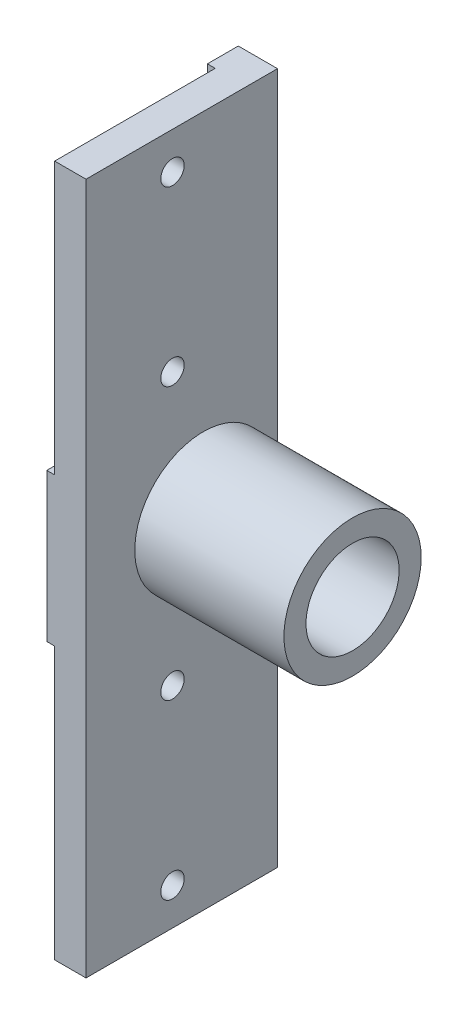
SolidWorks part; units mm, degrees
material "6061-T6 (SS)"
ref_plane "Front Plane" through (0, 0, 0) normal (0, 0, 1) x (1, 0, 0)
ref_plane "Top Plane" through (0, 0, 0) normal (0, 1, 0) x (1, 0, 0)
ref_plane "Right Plane" through (0, 0, 0) normal (1, 0, 0) x (0, 0, -1)
sketch "Sketch1" plane through (0, 0, 0) normal (1, 0, 0) x (0, 0, -1)
  line L0 (0, 0) -> (-63.5861, 0) construction
  line L1 (0, 0) -> (0, -23.8126) construction
  line L2 (12, 0) -> (12, 56)
  line L3 (12, 56) -> (-19, 56)
  line L4 (-19, 56) -> (-19, 0)
  line L5 (-19, 0) -> (12, 0)
  circle A1 centre (0, 0) radius 7.5413 construction
  dimension "D5" = 15.0825
  dimension "D3" = 31
  dimension "D4" = 112
  dimension "D6" = 12
extrude "Boss-Extrude1" add sketch "Sketch1" along normal blind 6.35
mirror "Mirror1" about plane through (0, 0, 0) normal (0, 1, 0) of "Boss-Extrude1"
sketch "Sketch2" plane through (6.35, 0, 0) normal (1, 0, 0) x (0, 0, -1)
  circle A0 centre (0, 0) radius 11.1125
  circle A2 centre (0, 0) radius 7.5413 construction
  dimension "D1" = 22.225
extrude "Boss-Extrude2" add sketch "Sketch2" along normal blind 24.1525
sketch "Sketch3" plane through (0, 0, 0) normal (-1, 0, 0) x (0, 0, 1)
  circle A0 centre (0, 0) radius 7.5413
  circle A1 centre (0, 0) radius 7.5413 construction
extrude "Cut-Extrude1" cut sketch "Sketch3" against normal through all
sketch "Sketch4" plane through (0, 0, 0) normal (-1, 0, 0) x (0, 0, 1)
  line L1 (19, 56) -> (-7, 56)
  line L2 (19, 56) -> (19, 12)
  line L3 (19, 12) -> (-7, 12)
  line L4 (-7, 56) -> (-7, 12)
  dimension "D1" = 26
  dimension "D2" = 44
extrude "Cut-Extrude2" cut sketch "Sketch4" against normal offset from surface (1.27 mm away) 5.08 up to face at (6.35, 0, 3.5)
fillet "Fillet1" radius 3.175 1 edges at (0.635, 12, -7)
mirror "Mirror2" about plane through (0, 0, 0) normal (0, 1, 0) of "Fillet1", "Cut-Extrude2"
hole_wizard "#10-24 Tapped Hole1" positions "Sketch6" profile "Sketch5" tap size "#10-24" standard "ANSI Inch"
sketch "Sketch6" plane through (1.27, 0, 0) normal (-1, 0, 0) x (0, 0, 1)
  line L0 (0, 0) -> (0, 15.0988) construction
  line L1 (5, 50) -> (5, 22) construction
  line L2 (0, 0) -> (30.2115, 0) construction
  point P0 (5, 50)
  point P2 (5, 22)
  dimension "D1" = 22
  dimension "D2" = 50
  dimension "D3" = 5
sketch "Sketch5" plane through (1.27, 50, 5) normal (0, 1, 0) x (0, 0, 1)
  line L0 (0, 0) -> (0, 16.0908)
  line L1 (0, 16.0908) -> (1.8986, 14.95)
  line L2 (1.8986, 14.95) -> (1.8986, 0)
  line L5 (1.8986, 0) -> (0, 0)
  line L10 (0, 16.0908) -> (-1.8987, 14.95) construction
  line L11 (0, -6.35) -> (0, 107.95) construction
  dimension "Tap Drill Dia." = 3.7973
  dimension "Tap Drill Depth" = 14.95
  dimension "Drill Angle" = 118
cosmetic thread "Hole Thread1" parameters "D1"=5.08, "D2"=4.826
cosmetic thread "Hole Thread2" parameters "D1"=5.08, "D2"=4.826
mirror "Mirror3" about plane through (0, 0, 0) normal (0, 1, 0) of "#10-24 Tapped Hole1"
